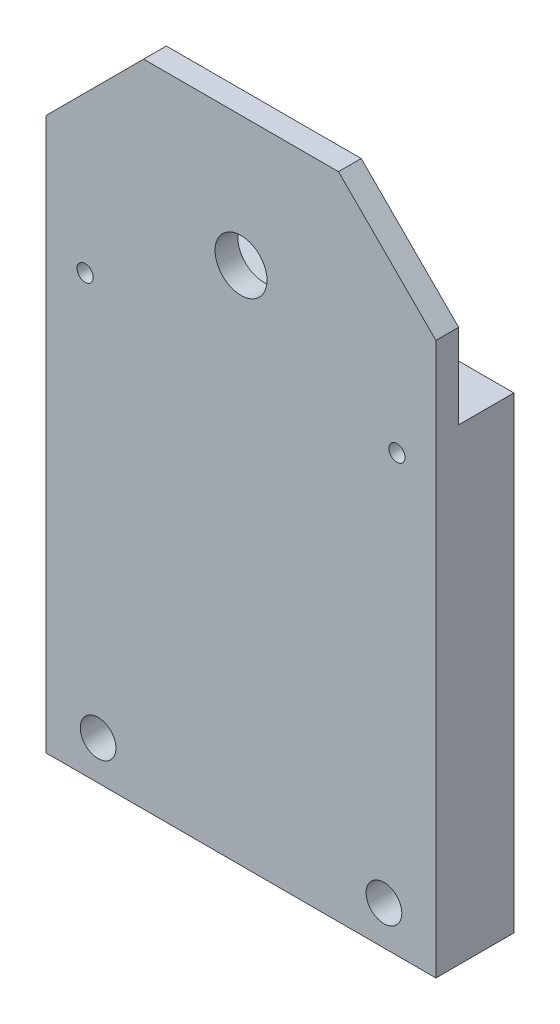
SolidWorks part; units mm, degrees
material "3.1325 (EN-AW 2017A)"
ref_plane "Plan de face" through (0, 0, 0) normal (0, 0, 1) x (1, 0, 0)
ref_plane "Plan de dessus" through (0, 0, 0) normal (0, 1, 0) x (1, 0, 0)
ref_plane "Plan de droite" through (0, 0, 0) normal (1, 0, 0) x (0, 0, -1)
sketch "Esquisse2" plane through (0, 0, 0) normal (0, 0, 1) x (1, 0, 0)
  line L1 (0, 0) -> (60, 0)
  line L2 (0, 0) -> (0, 100)
  line L3 (0, 100) -> (60, 100)
  line L4 (60, 0) -> (60, 100)
  dimension "D1" = 60
  dimension "D2" = 100
extrude "Boss.-Extru.1" add sketch "Esquisse2" along normal blind 12
sketch "Esquisse3" plane through (0, 0, 12) normal (0, 0, 1) x (1, 0, 0)
  line L3 (60, 100) -> (0, 100) construction
  circle A0 centre (30, 80) radius 4
  dimension "D1" = 20
extrude "Enlèv. mat.-Extru.1" cut sketch "Esquisse3" against normal blind 3.5
sketch "Esquisse5" plane through (0, 0, 0) normal (-1, 0, 0) x (0, 0, 1)
  line L0 (12, 100) -> (12, 0) construction
  line L1 (0, 100) -> (8.5, 100)
  line L2 (0, 100) -> (0, 72)
  line L3 (0, 72) -> (8.5, 72)
  line L4 (8.5, 100) -> (8.5, 72)
  line L5 (8.5, 80) -> (12, 80) construction
  dimension "D1" = 3.5
  dimension "D2" = 8
extrude "Enlèv. mat.-Extru.2" cut sketch "Esquisse5" against normal through all
hole_wizard "Trou taraudé M31" positions "Esquisse7" profile "Esquisse6" tap size "M3" standard "ISO" end condition through all
sketch "Esquisse7" plane through (0, 0, 12) normal (0, 0, 1) x (1, 0, 0)
  point P0 (54, 67)
  point P1 (30, 80)
  dimension "D1" = 24
  dimension "D2" = 13
sketch "Esquisse6" plane through (54, 67, 12) normal (1, 0, 0) x (0, -1, 0)
  line L0 (0, 0) -> (0, 12)
  line L1 (0, 12) -> (1.25, 12)
  line L2 (1.25, 12) -> (1.25, 0)
  line L5 (1.25, 0) -> (0, 0)
  line L11 (0, -6.35) -> (0, 107.95) construction
  dimension "Diamètre du trou pour taraudage jusqu'au prochain" = 2.5
  dimension "Profondeur du trou pour taraudage jusqu'au prochain" = 12
cosmetic thread "Filetage de perçage1" parameters "D2"=3
hole_wizard "Trou taraudé M32" positions "Esquisse9" profile "Esquisse8" tap size "M3" standard "ISO" end condition through all
sketch "Esquisse9" plane through (0, 0, 12) normal (0, 0, 1) x (1, 0, 0)
  circle A0 centre (54, 67) radius 1.25 construction
  circle A1 centre (30, 80) radius 4 construction
  point P0 (6, 67)
  dimension "D1" = 0
  dimension "D2" = 24
  dimension "D3" = 13
sketch "Esquisse8" plane through (6, 67, 12) normal (1, 0, 0) x (0, -1, 0)
  line L0 (0, 0) -> (0, 12)
  line L1 (0, 12) -> (1.25, 12)
  line L2 (1.25, 12) -> (1.25, 0)
  line L5 (1.25, 0) -> (0, 0)
  line L11 (0, -6.35) -> (0, 107.95) construction
  dimension "Diamètre du trou pour taraudage jusqu'au prochain" = 2.5
  dimension "Profondeur du trou pour taraudage jusqu'au prochain" = 12
cosmetic thread "Filetage de perçage2" parameters "D2"=3
hole_wizard "Chambrage pour vis à tête hexagonale M51" positions "Esquisse15" profile "Esquisse14" counterbore size "M5" standard "ISO" end condition through all
sketch "Esquisse15" plane through (0, 0, 0) normal (0, 0, -1) x (-1, 0, 0)
  line L0 (0, 0) -> (-60, 0) construction
  line L1 (0, 72) -> (0, 0) construction
  point P0 (-8, 6)
  dimension "D1" = 6
  dimension "D2" = 8
sketch "Esquisse14" plane through (8, 6, 0) normal (1, 0, 0) x (0, 1, 0)
  line L0 (0, 0) -> (0, 12)
  line L1 (0, 12) -> (2.75, 12)
  line L3 (2.75, 12) -> (2.75, 5)
  line L4 (2.75, 5) -> (5, 5)
  line L5 (5, 5) -> (5, 0)
  line L7 (5, 0) -> (0, 0)
  line L11 (0, -6.35) -> (0, 107.95) construction
  dimension "Diamètre du perçage jusqu'au prochain" = 5.5
  dimension "Profondeur du perçage jusqu'au prochain" = 12
  dimension "Diamètre du chambrage" = 10
  dimension "Profondeur du chambrage" = 5
hole_wizard "Chambrage pour vis à tête hexagonale M52" positions "Esquisse17" profile "Esquisse16" counterbore size "M5" standard "ISO" end condition through all
sketch "Esquisse17" plane through (0, 0, 0) normal (0, 0, -1) x (-1, 0, 0)
  line L0 (-60, 0) -> (-60, 72) construction
  line L1 (0, 0) -> (-60, 0) construction
  point P0 (-52, 6)
  dimension "D1" = 8
  dimension "D2" = 6
sketch "Esquisse16" plane through (52, 6, 0) normal (1, 0, 0) x (0, 1, 0)
  line L0 (0, 0) -> (0, 12)
  line L1 (0, 12) -> (2.75, 12)
  line L3 (2.75, 12) -> (2.75, 5)
  line L4 (2.75, 5) -> (5, 5)
  line L5 (5, 5) -> (5, 0)
  line L7 (5, 0) -> (0, 0)
  line L11 (0, -6.35) -> (0, 107.95) construction
  dimension "Diamètre du perçage jusqu'au prochain" = 5.5
  dimension "Profondeur du perçage jusqu'au prochain" = 12
  dimension "Diamètre du chambrage" = 10
  dimension "Profondeur du chambrage" = 5
chamfer "Chanfrein1" distance 15 angle 45 2 edges at (0, 100, 10.25) (60, 100, 10.25)
